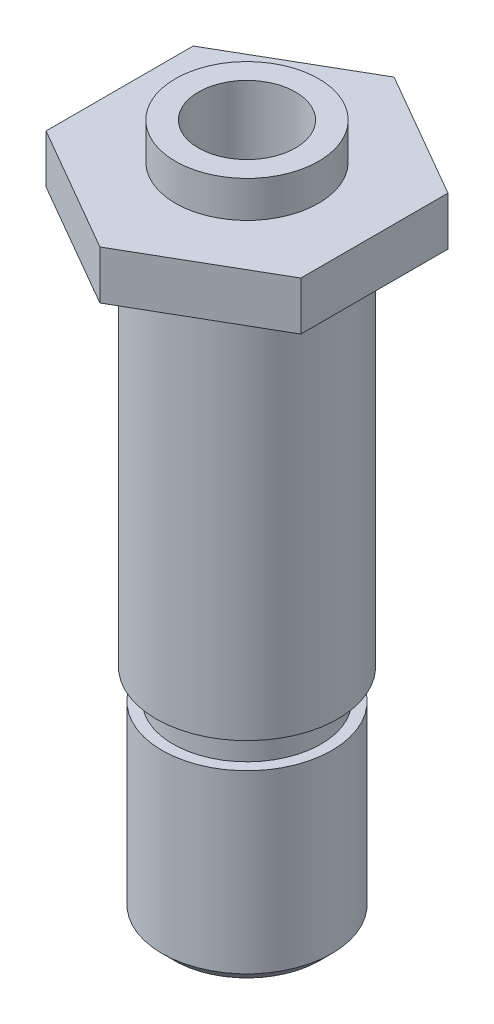
SolidWorks part; units mm, degrees
ref_plane "Спереди" through (0, 0, 0) normal (0, 0, 1) x (1, 0, 0)
ref_plane "Сверху" through (0, 0, 0) normal (0, 1, 0) x (1, 0, 0)
ref_plane "Справа" through (0, 0, 0) normal (1, 0, 0) x (0, 0, -1)
sketch "Эскиз1" plane through (0, 0, 0) normal (0, 1, 0) x (1, 0, 0)
  line L1 (10.5, -6.0622) -> (10.5, 6.0622)
  line L2 (10.5, 6.0622) -> (0, 12.1244)
  line L3 (0, 12.1244) -> (-10.5, 6.0622)
  line L4 (-10.5, 6.0622) -> (-10.5, -6.0622)
  line L5 (-10.5, -6.0622) -> (0, -12.1244)
  line L6 (0, -12.1244) -> (10.5, -6.0622)
  circle A0 centre (0, 0) radius 10.5 construction
extrude "Бобышка-Вытянуть1" add sketch "Эскиз1" along normal blind 4
sketch "Эскиз2" plane through (0, 4, 0) normal (0, 1, 0) x (1, 0, 0)
  circle A0 centre (0, 0) radius 5.9
extrude "Бобышка-Вытянуть2" add sketch "Эскиз2" along normal blind 3
sketch "Эскиз3" plane through (0, 0, 0) normal (0, -1, 0) x (1, 0, 0)
  circle A0 centre (0, 0) radius 7.5
extrude "Бобышка-Вытянуть3" add sketch "Эскиз3" along normal blind 50
sketch "Эскиз4" plane through (0, 7, 0) normal (0, 1, 0) x (1, 0, 0)
  circle A0 centre (0, 0) radius 4
extrude "Вырез-Вытянуть1" cut sketch "Эскиз4" against normal blind 35
sketch "Эскиз6" plane through (0, 0, 0) normal (1, 0, 0) x (0, 0, -1)
  line L0 (7.5, -50) -> (7.5, -32)
  line L1 (7.5, -32) -> (6.1, -32)
  line L2 (6.1, -32) -> (6.1, -34.5)
  line L3 (6.1, -34.5) -> (7, -34.5)
  line L4 (7, -34.5) -> (7, -50)
  line L5 (-7.5, -50) -> (7.5, -50) construction
  line L6 (7, -50) -> (7.5, -50)
  line L7 (0, -50.5265) -> (0, -31.0084) construction
  line L8 (7.5, -50) -> (7.5, 0) construction
revolve "Вырез-Повернуть1" cut sketch "Эскиз6" angle 360 about L7
sketch "Эскиз7" plane through (0, -50, 0) normal (0, -1, 0) x (1, 0, 0)
  circle A0 centre (0, 0) radius 2
extrude "Вырез-Вытянуть2" cut sketch "Эскиз7" against normal through all
chamfer "Фаска1" distance 1 angle 45 1 edges at (0, -50, -7)
